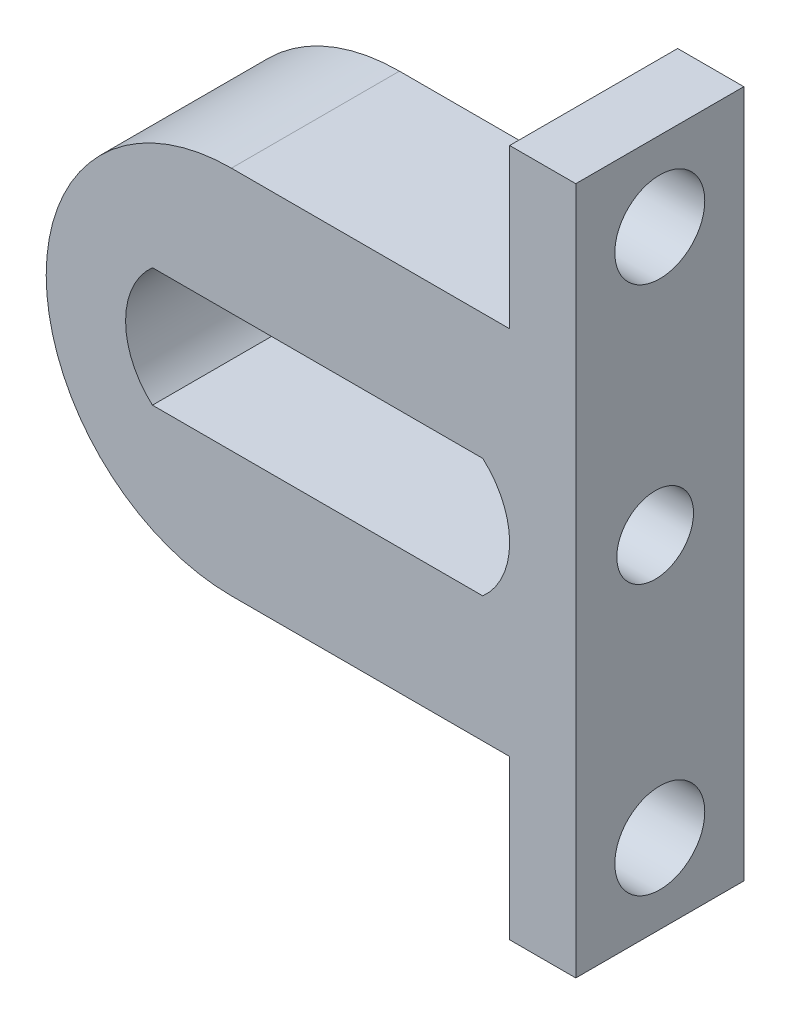
SolidWorks part; units mm, degrees
material "1060 Alloy"
ref_plane "Front Plane" through (0, 0, 0) normal (0, 0, 1) x (1, 0, 0)
ref_plane "Top Plane" through (0, 0, 0) normal (0, 1, 0) x (1, 0, 0)
ref_plane "Right Plane" through (0, 0, 0) normal (1, 0, 0) x (0, 0, -1)
sketch "Sketch1" plane through (0, 0, 0) normal (0, 0, 1) x (1, 0, 0)
  line L0 (515.21, 42.7906) -> (512.71, 42.7906) construction
  line L1 (512.71, 42.7906) -> (512.71, 48.7906) construction
  line L2 (512.71, 48.7906) -> (502.1943, 48.7906) construction
  line L3 (502.1943, 62.7906) -> (512.71, 62.7906) construction
  line L4 (512.71, 62.7906) -> (512.71, 68.7906) construction
  line L5 (515.21, 68.7906) -> (512.71, 68.7906) construction
  line L6 (515.21, 42.7906) -> (515.21, 68.7906) construction
  line L7 (511.6943, 53.5406) -> (499.21, 53.5406) construction
  line L8 (511.6943, 58.0406) -> (499.21, 58.0406) construction
  line L9 (515.21, 42.7906) -> (512.71, 42.7906)
  line L10 (512.71, 42.7906) -> (512.71, 48.7906)
  line L11 (512.71, 48.7906) -> (502.1943, 48.7906)
  line L12 (502.1943, 62.7906) -> (512.71, 62.7906)
  line L13 (512.71, 62.7906) -> (512.71, 68.7906)
  line L14 (515.21, 68.7906) -> (512.71, 68.7906)
  line L15 (515.21, 42.7906) -> (515.21, 68.7906)
  line L16 (511.6943, 53.5406) -> (499.21, 53.5406)
  line L17 (511.6943, 58.0406) -> (499.21, 58.0406)
  arc A0 (502.1943, 62.7906) -> (502.1943, 48.7906) centre (502.1943, 55.7906) ccw construction
  arc A1 (499.21, 58.0406) -> (499.21, 53.5406) centre (501.1943, 55.7906) ccw construction
  arc A2 (511.6943, 53.5406) -> (511.6943, 58.0406) centre (509.71, 55.7906) ccw construction
  arc A3 (502.1943, 62.7906) -> (502.1943, 48.7906) centre (502.1943, 55.7906) ccw
  arc A4 (499.21, 58.0406) -> (499.21, 53.5406) centre (501.1943, 55.7906) ccw
  arc A5 (511.6943, 53.5406) -> (511.6943, 58.0406) centre (509.71, 55.7906) ccw
extrude "Boss-Extrude1" add sketch "Sketch1" along normal blind 6.35
sketch "Sketch2" plane through (515.21, 0, 0) normal (1, 0, 0) x (0, 0, -1)
  circle A0 centre (-3.175, 45.7906) radius 1.7
  circle A1 centre (-3.35, 55.7906) radius 1.45
  circle A2 centre (-3.175, 65.7906) radius 1.7
  circle A4 centre (-3.175, 45.7906) radius 1.25 construction
  circle A5 centre (-3.175, 65.7906) radius 1.25 construction
  circle A6 centre (-3.35, 55.7906) radius 1.1 construction
  dimension "D1" = 2.9
  dimension "D2" = 3.4
  dimension "D3" = 3.4
extrude "Cut-Extrude1" cut sketch "Sketch2" against normal up to next
